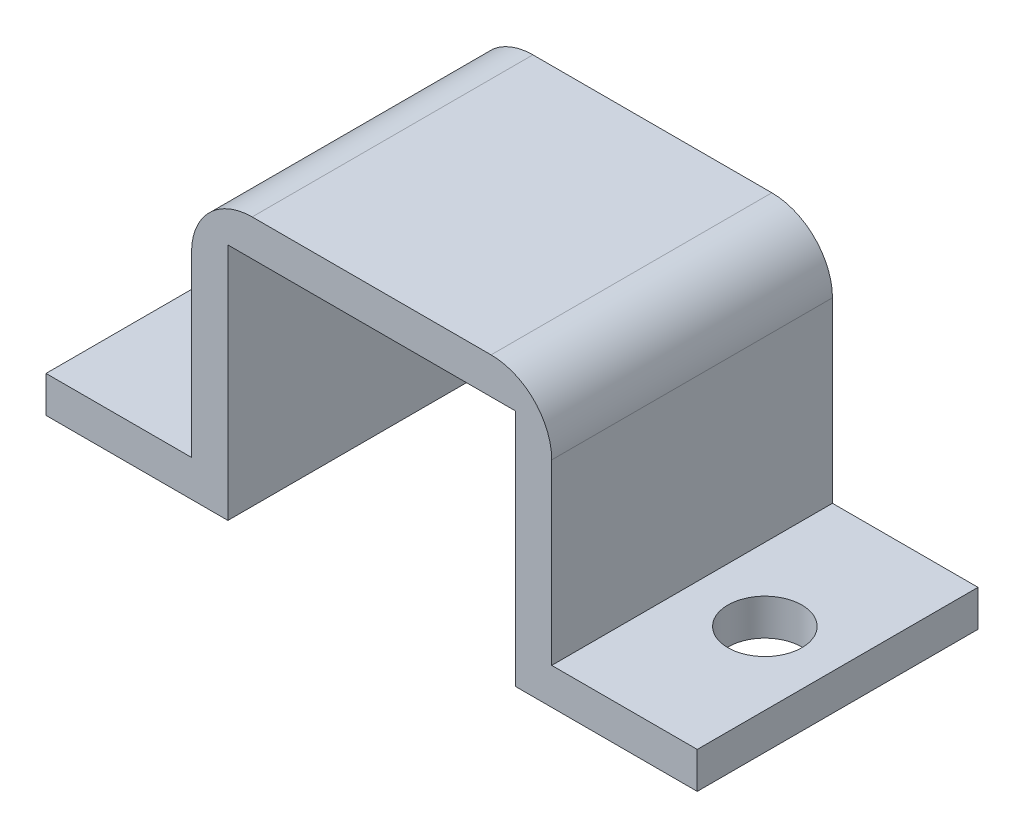
SolidWorks part; units mm, degrees
ref_plane "Front Plane" through (0, 0, 0) normal (0, 0, 1) x (1, 0, 0)
ref_plane "Top Plane" through (0, 0, 0) normal (0, 1, 0) x (1, 0, 0)
ref_plane "Right Plane" through (0, 0, 0) normal (1, 0, 0) x (0, 0, -1)
sketch "Sketch2" plane through (0, 0, 0) normal (0, 0, 1) x (1, 0, 0)
  line L0 (0, 0) -> (7.62, 0)
  line L1 (7.62, 0) -> (7.62, 9.9949)
  line L2 (7.62, 9.9949) -> (19.6596, 9.9949)
  line L3 (19.6596, 9.9949) -> (19.6596, 0)
  line L4 (19.6596, 0) -> (27.2796, 0)
  line L5 (0, 1.524) -> (6.096, 1.524)
  line L6 (6.096, 1.524) -> (6.096, 11.5189)
  line L7 (6.096, 11.5189) -> (21.1836, 11.5189)
  line L8 (21.1836, 11.5189) -> (21.1836, 1.524)
  line L9 (21.1836, 1.524) -> (27.2796, 1.524)
  line L10 (0, 1.524) -> (0, 0)
  line L11 (27.2796, 1.524) -> (27.2796, 0)
  dimension "D1" = 9.9949
  dimension "D2" = 7.62
  dimension "D3" = 7.62
  dimension "D4" = 12.0396
  dimension "D5" = 1.524
extrude "Boss-Extrude1" add sketch "Sketch2" along normal blind 11.7602
fillet "Fillet2" radius 2.54 1 edges at (21.1836, 11.5189, 5.8801)
fillet "Fillet3" radius 2.54 1 edges at (6.096, 11.5189, 5.8801)
sketch "Sketch3" plane through (0, 0, 0) normal (0, 1, 0) x (1, 0, 0)
  line L0 (0, -5.8801) -> (6.096, -5.8801) construction
  line L1 (0, -11.7602) -> (0, 0) construction
  line L2 (6.096, -5.8801) -> (27.826, -5.8801) construction
  line L3 (27.2796, -11.7602) -> (27.2796, 0) construction
  line L4 (0, -11.7602) -> (0, 0) construction
  circle A0 centre (3.048, -5.8801) radius 1.55
  circle A1 centre (24.2316, -5.8801) radius 1.55
  dimension "D3" = 3.1
  dimension "D4" = 3.1
  dimension "D1" = 3.048
  dimension "D2" = 3.048
extrude "Cut-Extrude1" cut sketch "Sketch3" along normal up to surface (1.524 mm away) up to face at (3.048, 1.524, 5.8801)
